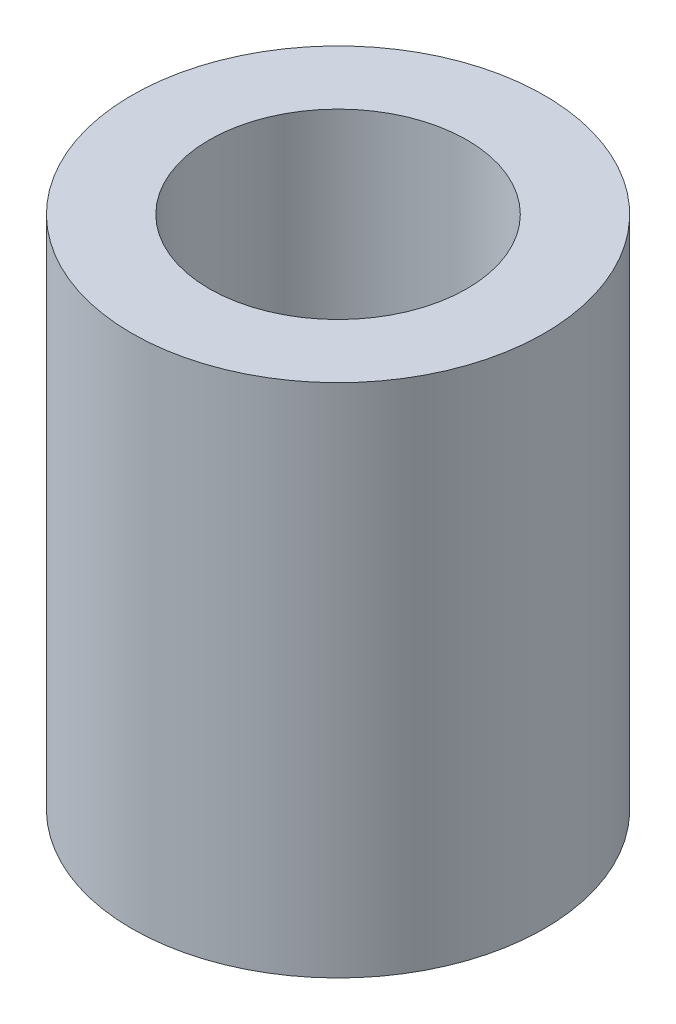
SolidWorks part; units mm, degrees
ref_plane "Front Plane" through (0, 0, 0) normal (0, 0, 1) x (1, 0, 0)
ref_plane "Top Plane" through (0, 0, 0) normal (0, 1, 0) x (1, 0, 0)
ref_plane "Right Plane" through (0, 0, 0) normal (1, 0, 0) x (0, 0, -1)
sketch "Sketch1" plane through (0, 0, 0) normal (0, 1, 0) x (1, 0, 0)
  circle A0 centre (0, 0) radius 5.08
  dimension "D1" = 10.16
extrude "Boss-Extrude1" add sketch "Sketch1" along normal blind 12.7
sketch "Sketch2" plane through (0, 0, 0) normal (0, -1, 0) x (1, 0, 0)
  circle A0 centre (0, 0) radius 3.175
  dimension "D1" = 6.35
extrude "Cut-Extrude1" cut sketch "Sketch2" against normal through all
